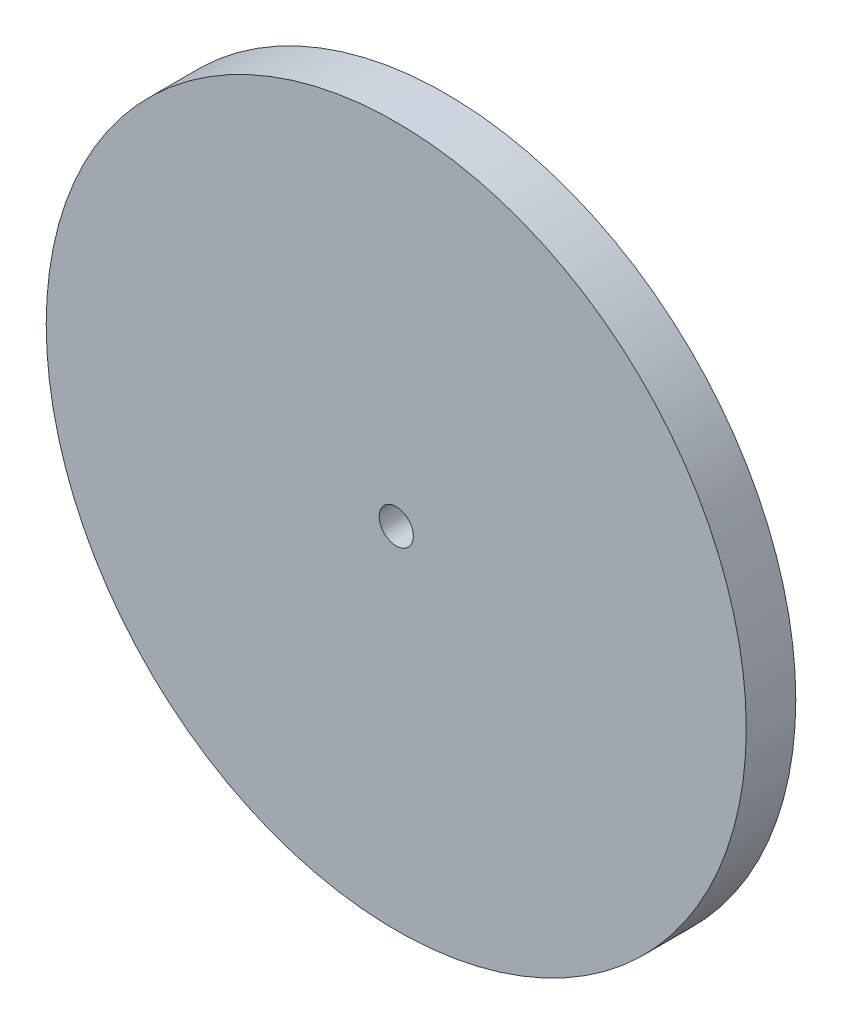
SolidWorks part; units mm, degrees
ref_plane "Front" through (0, 0, 0) normal (0, 0, 1) x (1, 0, 0)
ref_plane "Top" through (0, 0, 0) normal (0, 1, 0) x (1, 0, 0)
ref_plane "Right" through (0, 0, 0) normal (1, 0, 0) x (0, 0, -1)
sketch "Sketch1" plane through (0, 0, 0) normal (0, 0, 1) x (1, 0, 0)
  circle A0 centre (0, 0) radius 41
  circle A1 centre (0, 0) radius 2
  dimension "D1" = 82
  dimension "D2" = 4
extrude "Boss-Extrude1" add sketch "Sketch1" along normal blind 5.8
